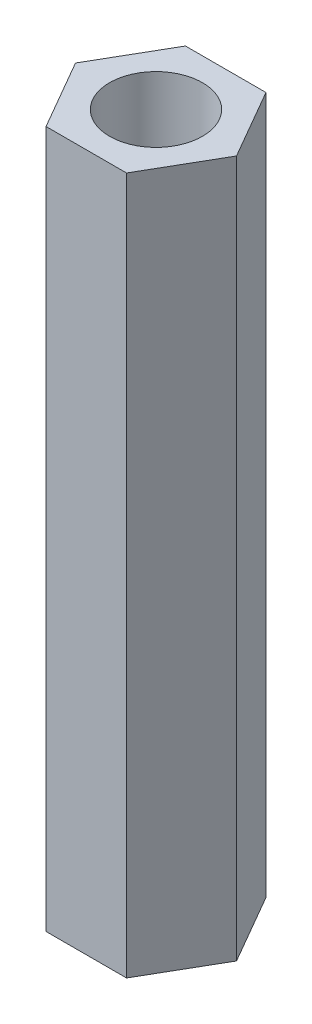
SolidWorks part; units mm, degrees
ref_plane "Front Plane" through (0, 0, 0) normal (0, 0, 1) x (1, 0, 0)
ref_plane "Top Plane" through (0, 0, 0) normal (0, 1, 0) x (1, 0, 0)
ref_plane "Right Plane" through (0, 0, 0) normal (1, 0, 0) x (0, 0, -1)
sketch "Sketch1" plane through (0, 0, 0) normal (0, 1, 0) x (1, 0, 0)
  line L1 (3.4641, 0) -> (1.7321, 3)
  line L2 (1.7321, 3) -> (-1.7321, 3)
  line L3 (-1.7321, 3) -> (-3.4641, 0)
  line L4 (-3.4641, 0) -> (-1.7321, -3)
  line L5 (-1.7321, -3) -> (1.7321, -3)
  line L6 (1.7321, -3) -> (3.4641, 0)
  circle A0 centre (0, 0) radius 3 construction
  circle A1 centre (0, 0) radius 2
  dimension "D1" = 4
  dimension "D2" = 6
extrude "Boss-Extrude1" add sketch "Sketch1" along normal blind 30
